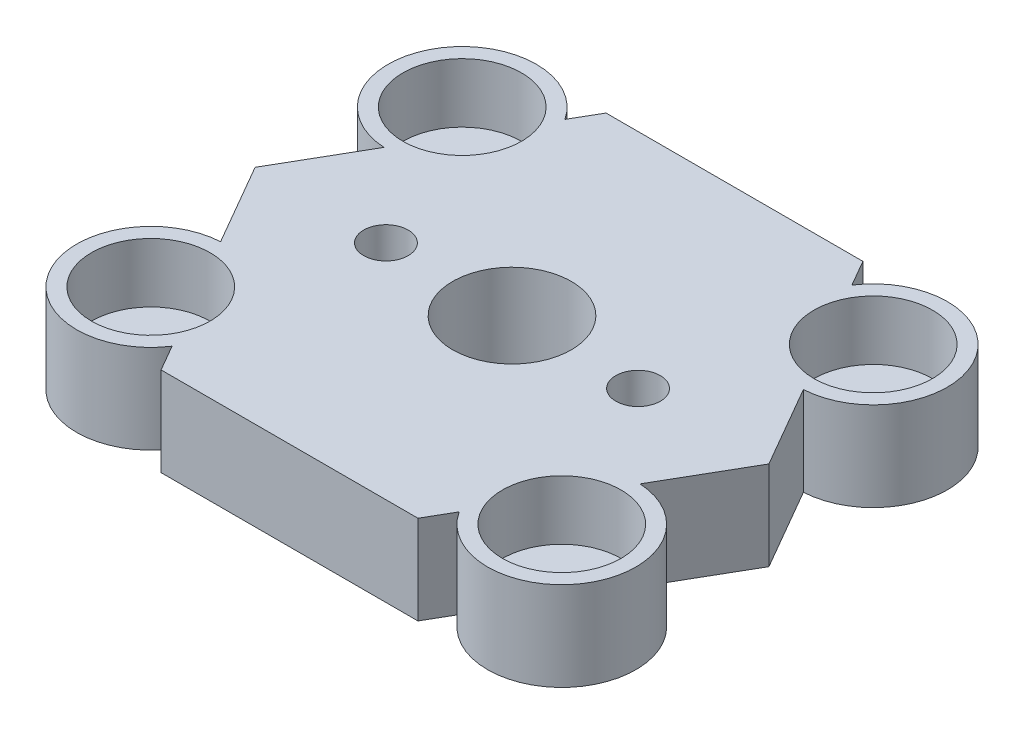
SolidWorks part; units mm, degrees
ref_plane "Front Plane" through (0, 0, 0) normal (0, 0, 1) x (1, 0, 0)
ref_plane "Top Plane" through (0, 0, 0) normal (0, 1, 0) x (1, 0, 0)
ref_plane "Right Plane" through (0, 0, 0) normal (1, 0, 0) x (0, 0, -1)
sketch "Sketch2" plane through (0, 0, 0) normal (0, 1, 0) x (1, 0, 0)
  line L0 (-8.5, 0) -> (8.5, 0) construction
  line L1 (0, 20.1846) -> (0, -20.1846) construction
  line L2 (-13.8564, 6) -> (-13.8564, 15) construction
  line L3 (17.3205, 0) -> (8.6603, 15)
  line L4 (8.6603, 15) -> (-8.6603, 15)
  line L5 (-8.6603, 15) -> (-17.3205, 0)
  line L6 (-17.3205, 0) -> (-8.6603, -15)
  line L7 (-8.6603, -15) -> (8.6603, -15)
  line L8 (8.6603, -15) -> (17.3205, 0)
  line L9 (-8.6603, 15) -> (-13.8564, 15) construction
  circle A0 centre (0, 0) radius 4
  circle A1 centre (8.5, 0) radius 1.5
  circle A2 centre (-8.5, 0) radius 1.5
  circle A3 centre (0, 0) radius 15 construction
  circle A4 centre (-13.8564, 10.5) radius 5
  circle A5 centre (-13.8564, 10.5) radius 1.5
  circle A6 centre (13.8564, 10.5) radius 1.5
  circle A7 centre (13.8564, 10.5) radius 5
  circle A8 centre (13.8564, -10.5) radius 1.5
  circle A9 centre (13.8564, -10.5) radius 5
  circle A10 centre (-13.8564, -10.5) radius 5
  circle A11 centre (-13.8564, -10.5) radius 1.5
  point P7 (0, 0)
  point P8 (0, 0)
  dimension "D1" = 8
  dimension "D3" = 3
  dimension "D4" = 3
  dimension "D6" = 10
  dimension "D7" = 3
  dimension "D2" = 17
  dimension "D5" = 30
  dimension "D8" = 9
extrude "Boss-Extrude1" add sketch "Sketch2" along normal blind 6 contours A4 | L3 L4 L5 L6 L7 L8 | A10 | A9 | A7 | A6 | A5 | A0 | A1 | A2 | A11 | A8
sketch "Sketch3" plane through (0, 0, 0) normal (0, -1, 0) x (1, 0, 0)
  circle A0 centre (-8.5, 0) radius 3.5
  circle A1 centre (8.5, 0) radius 3.5
  dimension "D1" = 7
  dimension "D2" = 7
extrude "Cut-Extrude3" cut sketch "Sketch3" against normal blind 3 contours A0 | A1
sketch "Sketch4" plane through (0, 6, 0) normal (0, 1, 0) x (1, 0, 0)
  circle A0 centre (-13.8564, 10.5) radius 4
  circle A1 centre (13.8564, 10.5) radius 4
  circle A2 centre (-13.8564, -10.5) radius 4
  circle A3 centre (13.8564, -10.5) radius 4
  dimension "D1" = 8
  dimension "D2" = 8
  dimension "D3" = 8
  dimension "D4" = 8
extrude "Cut-Extrude4" cut sketch "Sketch4" against normal blind 4
